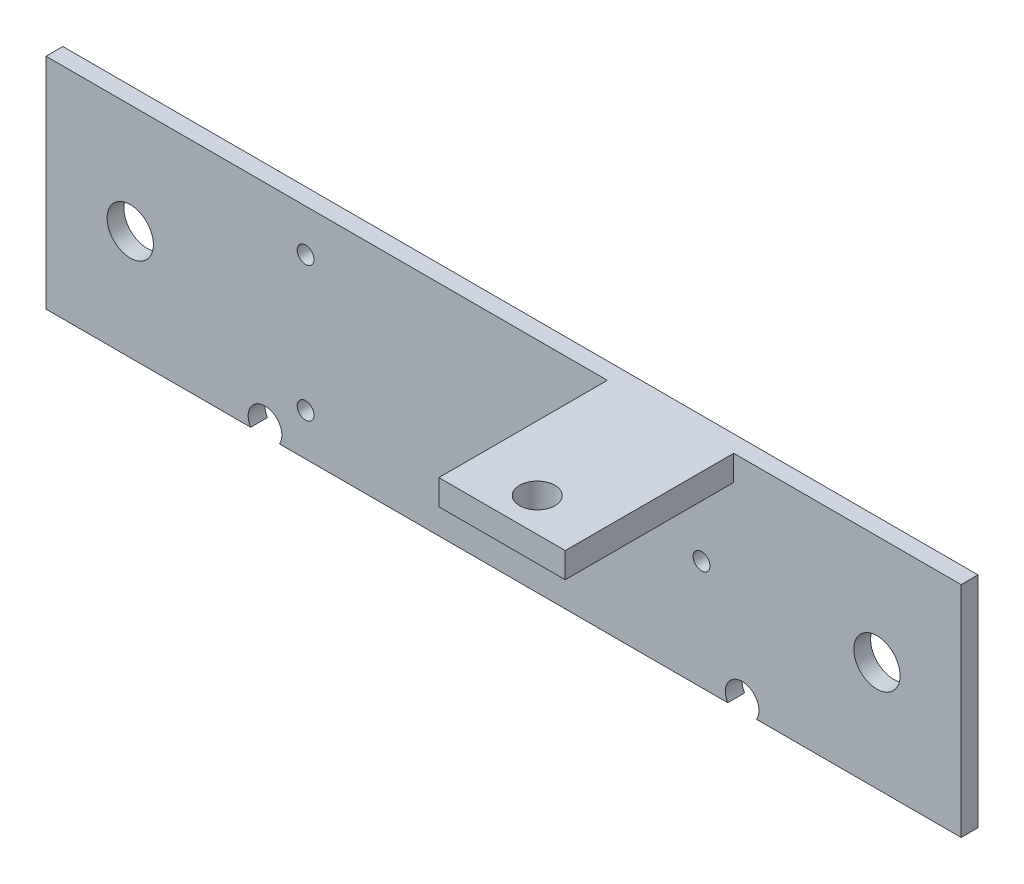
SolidWorks part; units mm, degrees
ref_plane "Front Plane" through (0, 0, 0) normal (0, 0, 1) x (1, 0, 0)
ref_plane "Top Plane" through (0, 0, 0) normal (0, 1, 0) x (1, 0, 0)
ref_plane "Right Plane" through (0, 0, 0) normal (1, 0, 0) x (0, 0, -1)
sketch "Sketch1" plane through (0, 0, 0) normal (0, 0, 1) x (1, 0, 0)
  line L0 (30.82, 21) -> (30.82, 5) construction
  line L1 (0, 0) -> (108.64, 0)
  line L2 (0, 0) -> (0, 26)
  line L3 (0, 26) -> (108.64, 26)
  line L4 (108.64, 0) -> (108.64, 26)
  line L5 (108.64, 13) -> (0, 13) construction
  circle A0 centre (30.82, 21) radius 1
  circle A1 centre (30.82, 5) radius 1
  circle A2 centre (77.82, 13) radius 1
  circle A3 centre (10, 13) radius 2.75
  circle A4 centre (98.64, 13) radius 2.75
  point P11 (30.82, 13)
  point P12 (0, 13)
  point P17 (108.64, 13)
  dimension "D9" = 2
  dimension "D10" = 2
  dimension "D11" = 2
  dimension "D12" = 16
  dimension "D3" = 5.5
  dimension "D4" = 5.5
  dimension "D1" = 108.64
  dimension "D2" = 26
  dimension "D5" = 47
  dimension "D6" = 30.82
  dimension "D7" = 30.82
  dimension "D13" = 10
  dimension "D14" = 10
extrude "Boss-Extrude1" add sketch "Sketch1" along normal blind 2
sketch "Sketch3" plane through (0, 0, 2) normal (0, 0, 1) x (1, 0, 0)
  line L0 (108.64, 26) -> (0, 26) construction
  line L1 (66.64, 26) -> (81.64, 26)
  line L2 (66.64, 26) -> (66.64, 23)
  line L3 (66.64, 23) -> (81.64, 23)
  line L4 (81.64, 26) -> (81.64, 23)
  line L5 (108.64, 0) -> (108.64, 26) construction
  dimension "D1" = 3
  dimension "D2" = 15
  dimension "D3" = 27
sketch "Sketch5" plane through (0, 0, 2) normal (0, 0, 1) x (1, 0, 0)
  line L0 (108.64, 0) -> (108.64, 26) construction
  line L1 (0, 26) -> (0, 0) construction
  circle A0 centre (26, 1.0435) radius 2
  circle A1 centre (82.64, 1.0435) radius 2
  dimension "D2" = 4
  dimension "D3" = 4
  dimension "D1" = 26
  dimension "D4" = 26
extrude "Cut-Extrude2" cut sketch "Sketch5" against normal up to next
extrude "Boss-Extrude2" add sketch "Sketch3" along normal blind 20
sketch "Sketch4" plane through (0, 26, 0) normal (0, 1, 0) x (1, 0, 0)
  line L1 (81.64, -22) -> (66.64, -22) construction
  line L2 (54.32, 0) -> (54.32, -2) construction
  line L4 (108.64, 0) -> (0, 0) construction
  line L5 (66.64, -2) -> (0, -2) construction
  circle A0 centre (74.32, -18) radius 2.1
  dimension "D1" = 4
  dimension "D3" = 4.2
  dimension "D2" = 20
extrude "Cut-Extrude1" cut sketch "Sketch4" against normal blind 15
